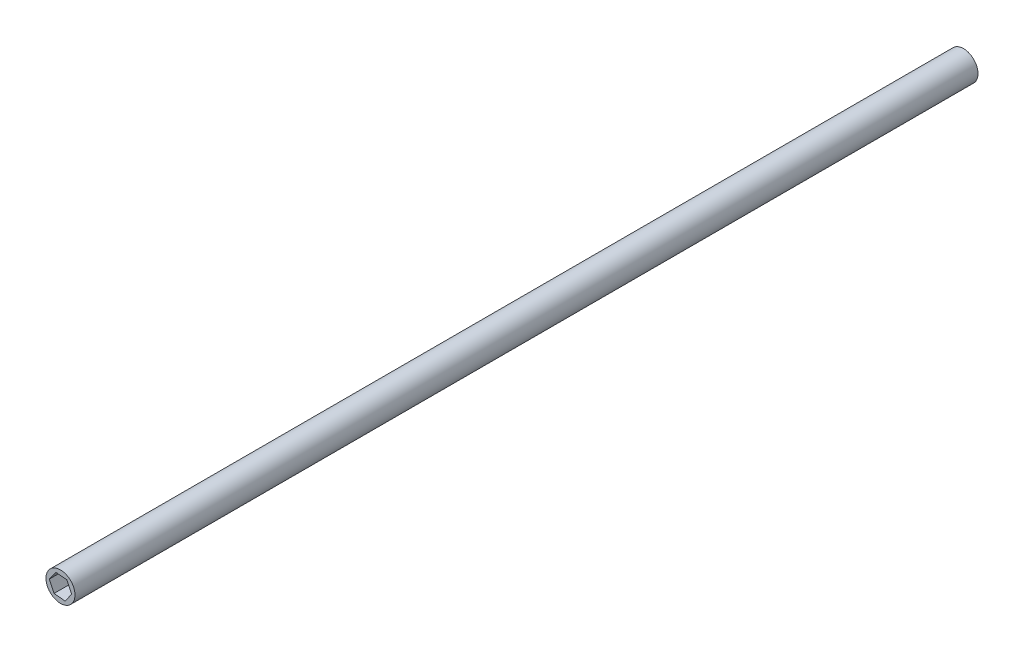
SolidWorks part; units mm, degrees
material "201 Annealed Stainless Steel (SS)"
ref_plane "Front Plane" through (0, 0, 0) normal (0, 0, 1) x (1, 0, 0)
ref_plane "Top Plane" through (0, 0, 0) normal (0, 1, 0) x (1, 0, 0)
ref_plane "Right Plane" through (0, 0, 0) normal (1, 0, 0) x (0, 0, -1)
sketch "Sketch1" plane through (0, 0, 0) normal (0, 0, 1) x (1, 0, 0)
  line L1 (7.6655, -0.7063) -> (4.4445, 6.2854)
  line L2 (4.4445, 6.2854) -> (-3.2211, 6.9917)
  line L3 (-3.2211, 6.9917) -> (-7.6655, 0.7063)
  line L4 (-7.6655, 0.7063) -> (-4.4445, -6.2854)
  line L5 (-4.4445, -6.2854) -> (3.2211, -6.9917)
  line L6 (3.2211, -6.9917) -> (7.6655, -0.7063)
  circle A0 centre (0, 0) radius 10
  circle A2 centre (0, 0) radius 6.6667 construction
  dimension "D1" = 20
extrude "Boss-Extrude1" add sketch "Sketch1" along normal blind 600
sketch "Sketch2" plane through (0, 0, 0) normal (0, 0, 1) x (1, 0, 0)
  circle A0 centre (0, 0) radius 10
extrude "Boss-Extrude2" add sketch "Sketch2" against normal blind 22.5
